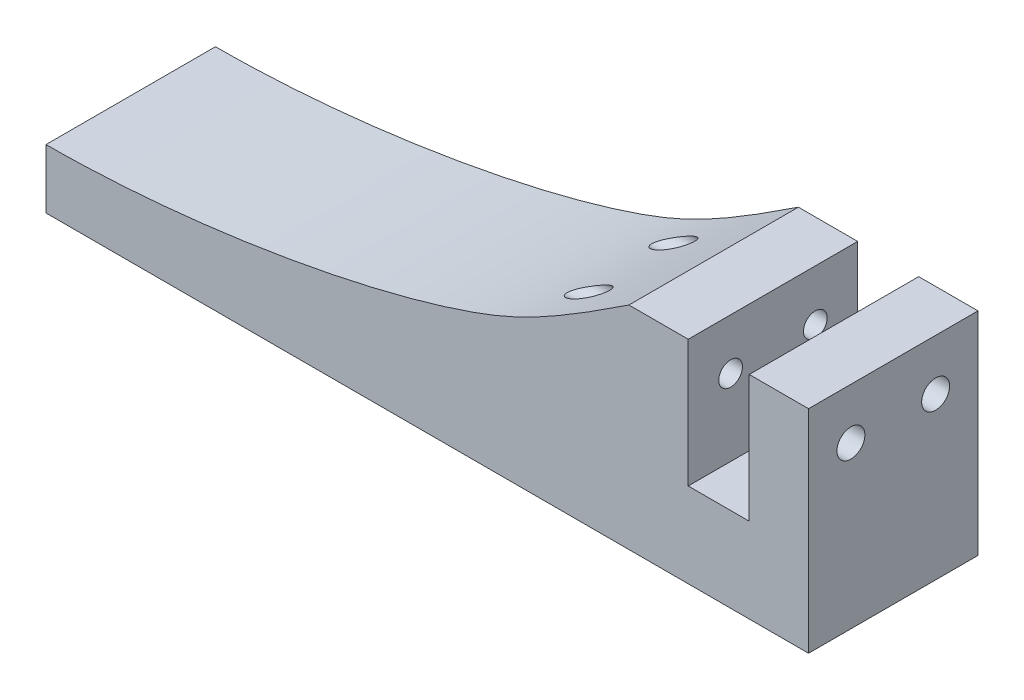
SolidWorks part; units mm, degrees
ref_plane "Front Plane" through (0, 0, 0) normal (0, 0, 1) x (1, 0, 0)
ref_plane "Top Plane" through (0, 0, 0) normal (0, 1, 0) x (1, 0, 0)
ref_plane "Right Plane" through (0, 0, 0) normal (1, 0, 0) x (0, 0, -1)
sketch "Sketch1" plane through (0, 0, 0) normal (0, 0, 1) x (1, 0, 0)
  line L0 (0, 123.3955) -> (0, 108.3955)
  line L1 (0, 108.3955) -> (-7.2, 108.3955)
  line L2 (-7.2, 108.3955) -> (-7.2, 123.3955)
  line L3 (-7.2, 123.3955) -> (-14.2, 123.3955)
  line L5 (-83, 105.3955) -> (-83, 98.3955)
  line L6 (-83, 98.3955) -> (7, 98.3955)
  line L7 (7, 98.3955) -> (7, 123.3955)
  line L8 (7, 123.3955) -> (0, 123.3955)
  line L9 (-83, 105.3955) -> (-49.9151, 105.3955) construction
  line L10 (-96.0454, 105.3955) -> (-69.9517, 105.3955) construction
  spline S0 degree 3 poles (-14.2, 123.3955) (-23.5306, 117.2056) (-38.4462, 109.9159) (-66.6915, 105.3955) (-83, 105.3955) knots 0 0 0 0 0.267224 1 1 1 1
  point P13 (-32.454, 113.5074)
  point P15 (0, 0)
  dimension "D1" = 7.2
  dimension "D2" = 7
  dimension "D3" = 15
  dimension "D4" = 10
  dimension "D5" = 90
  dimension "D6" = 7
extrude "Boss-Extrude1" add sketch "Sketch1" along normal blind 20
sketch "Sketch2" plane through (7, 0, 0) normal (1, 0, 0) x (0, 0, -1)
  line L0 (-20, 117.3955) -> (0, 117.3955) construction
  line L1 (-20, 98.3955) -> (-20, 123.3955) construction
  line L2 (0, 98.3955) -> (0, 123.3955) construction
  line L3 (-10, 123.3955) -> (-10, 114.7664) construction
  line L4 (-20, 123.3955) -> (0, 123.3955) construction
  circle A0 centre (-15, 117.3955) radius 1.65
  circle A1 centre (-5, 117.3955) radius 1.65
  dimension "D1" = 3.3
  dimension "D2" = 10
  dimension "D3" = 6
extrude "Cut-Extrude1" cut sketch "Sketch2" against normal up to surface (7 mm away) up to face at (0, 115.8955, 10)
sketch "Sketch3" plane through (-7.2, 0, 0) normal (1, 0, 0) x (0, 0, -1)
  circle A0 centre (-15, 117.3955) radius 1.4
  circle A1 centre (-5, 117.3955) radius 1.4
  dimension "D1" = 2.8
extrude "Cut-Extrude2" cut sketch "Sketch3" against normal blind 27
